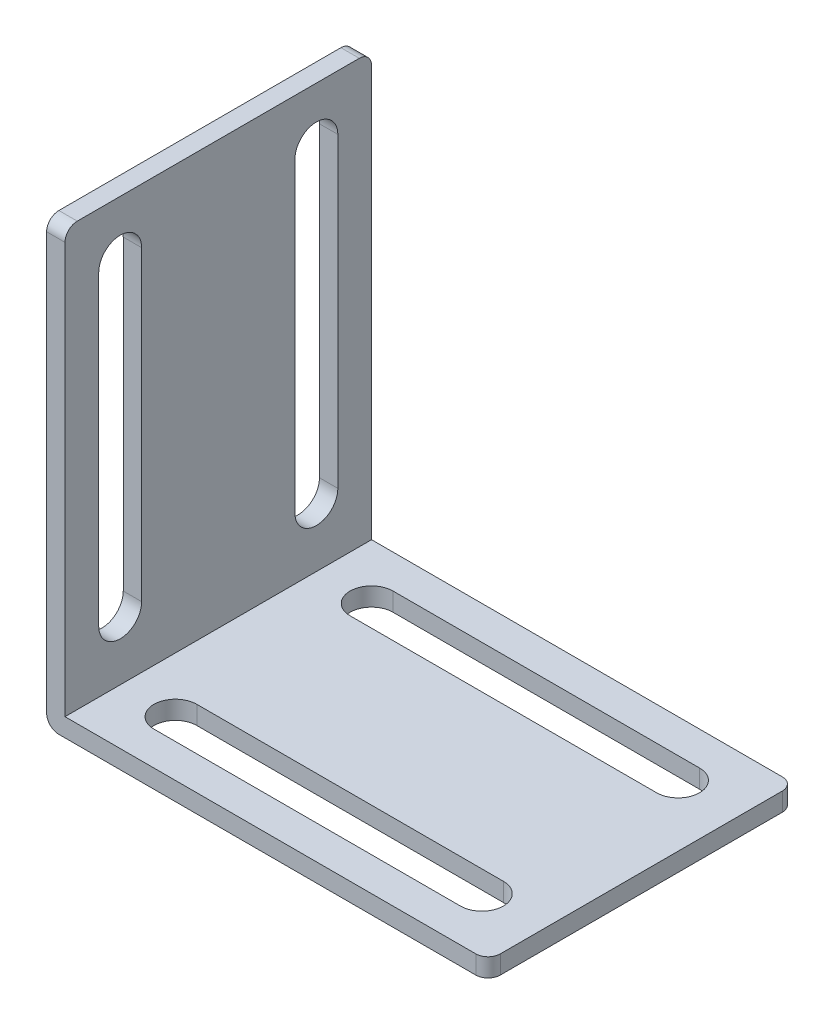
SolidWorks part; units mm, degrees
ref_plane "Front Plane" through (0, 0, 0) normal (0, 0, 1) x (1, 0, 0)
ref_plane "Top Plane" through (0, 0, 0) normal (0, 1, 0) x (1, 0, 0)
ref_plane "Right Plane" through (0, 0, 0) normal (1, 0, 0) x (0, 0, -1)
sketch "Sketch1" plane through (0, 0, 0) normal (0, 1, 0) x (1, 0, 0)
  line L1 (0, 0) -> (36, 0)
  line L2 (0, 0) -> (0, 25)
  line L3 (0, 25) -> (36, 25)
  line L4 (36, 0) -> (36, 25)
  dimension "D1" = 25
  dimension "D2" = 36
extrude "Boss-Extrude1" add sketch "Sketch1" along normal blind 36
sketch "Sketch2" plane through (0, 36, 0) normal (0, 1, 0) x (1, 0, 0)
  line L0 (36, 25) -> (0, 25) construction
  line L1 (1.5, 25) -> (36, 25)
  line L2 (1.5, 25) -> (1.5, 0)
  line L3 (1.5, 0) -> (36, 0)
  line L4 (36, 25) -> (36, 0)
  dimension "D1" = 1.5
extrude "Cut-Extrude1" cut sketch "Sketch2" against normal blind 34.5
fillet "Fillet1" radius 1 5 edges at (0, 0, -12.5) (0.75, 36, 0) (0.75, 36, -25) (36, 0.75, -25) (36, 0.75, 0)
sketch "Sketch3" plane through (0, 1.5, 0) normal (0, 1, 0) x (1, 0, 0)
  line L0 (1.5, 0) -> (35, 0) construction
  line L1 (1.5, 25) -> (1.5, 0) construction
  line L2 (6, 2.75) -> (31, 2.75)
  line L3 (6, 6.25) -> (31, 6.25)
  line L4 (6, 18.75) -> (31, 18.75)
  line L5 (6, 22.25) -> (31, 22.25)
  circle A0 centre (6, 4.5) radius 1.75
  circle A1 centre (31, 4.5) radius 1.75
  circle A2 centre (31, 20.5) radius 1.75
  circle A3 centre (6, 20.5) radius 1.75
  dimension "D1" = 3.5
  dimension "D2" = 4.5
  dimension "D3" = 4.5
  dimension "D4" = 2
  dimension "D5" = 2
extrude "Cut-Extrude2" cut sketch "Sketch3" against normal blind 1.5 contours A1 L3 A0 L2 | A0 | A3 L4 A2 L5 | A2 | A1
sketch "Sketch4" plane through (1.5, 0, 0) normal (1, 0, 0) x (0, 0, -1)
  line L0 (24, 36) -> (1, 36) construction
  line L1 (0, 1.5) -> (0, 35) construction
  line L2 (18.75, 31.5) -> (18.75, 6.5)
  line L3 (22.25, 31.5) -> (22.25, 6.5)
  line L4 (6.25, 31.5) -> (6.25, 6.5)
  line L5 (2.75, 31.5) -> (2.75, 6.5)
  circle A0 centre (4.5, 31.5) radius 1.75
  circle A1 centre (20.5, 31.5) radius 1.75
  circle A2 centre (20.5, 6.5) radius 1.75
  circle A3 centre (4.5, 6.5) radius 1.75
  dimension "D1" = 3.5
  dimension "D2" = 4.5
  dimension "D3" = 4.5
  dimension "D6" = 25
  dimension "D7" = 16
  dimension "D4" = 2
  dimension "D5" = 2
extrude "Cut-Extrude3" cut sketch "Sketch4" against normal blind 1.5 contours A3 L4 A0 L5 | A0 | A1 | A2 L3 A1 L2 | A2
